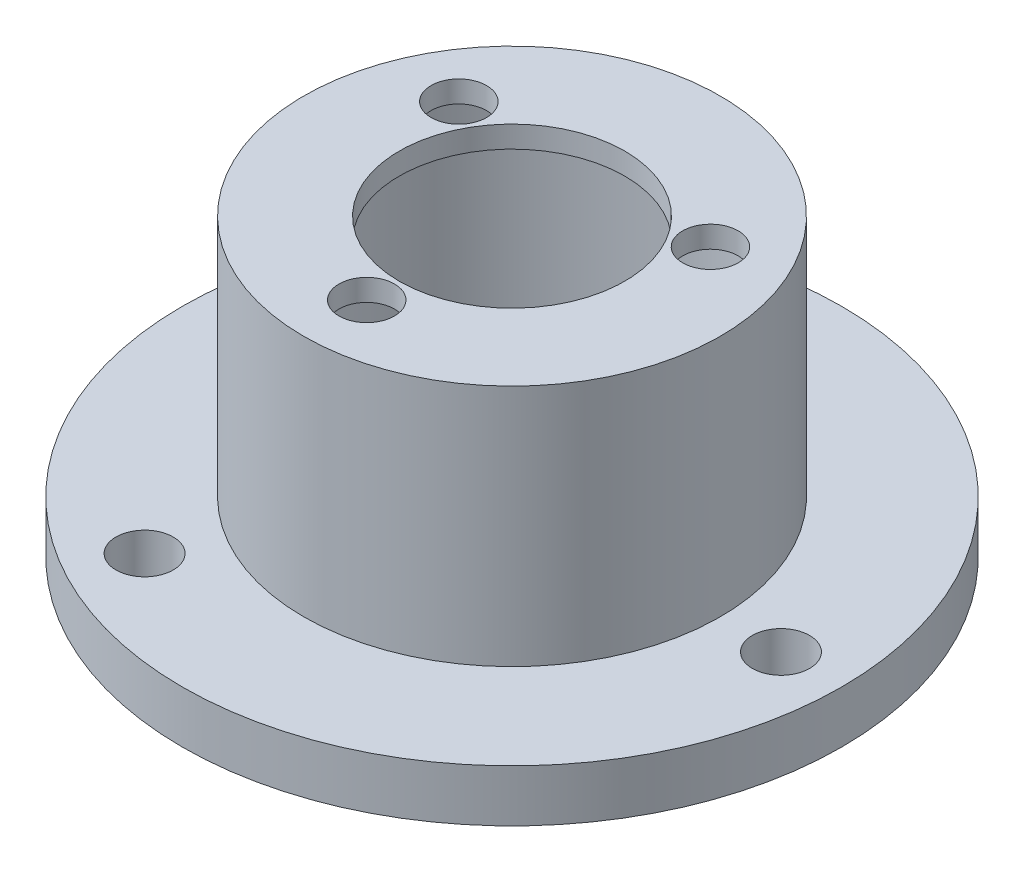
SolidWorks part; units mm, degrees
ref_plane "Front Plane" through (0, 0, 0) normal (0, 0, 1) x (1, 0, 0)
ref_plane "Top Plane" through (0, 0, 0) normal (0, 1, 0) x (1, 0, 0)
ref_plane "Right Plane" through (0, 0, 0) normal (1, 0, 0) x (0, 0, -1)
sketch "Sketch1" plane through (0, 0, 0) normal (0, 1, 0) x (1, 0, 0)
  circle A0 centre (0, 0) radius 11
  circle A1 centre (0, 0) radius 19
  dimension "D1" = 22
  dimension "D2" = 8
extrude "Boss-Extrude1" add sketch "Sketch1" along normal blind 3
sketch "Sketch2" plane through (0, 3, 0) normal (0, 1, 0) x (1, 0, 0)
  circle A0 centre (0, 0) radius 12
  circle A1 centre (0, 0) radius 11
  circle A2 centre (0, 0) radius 11 construction
  dimension "D1" = 1
extrude "Boss-Extrude2" add sketch "Sketch2" along normal blind 14
sketch "Sketch3" plane through (0, 17, 0) normal (0, 1, 0) x (1, 0, 0)
  circle A0 centre (0, 0) radius 12
  circle A1 centre (0, 0) radius 6.5
  circle A2 centre (0, 0) radius 12 construction
  dimension "D1" = 13
extrude "Boss-Extrude3" add sketch "Sketch3" against normal blind 1.25
sketch "Sketch6" plane through (0, 17, 0) normal (0, 1, 0) x (1, 0, 0)
  point P0 (-7.25, 4.1859)
  point P2 (7.25, 4.1859)
  point P4 (0, -8.3715)
  point P7 (0, 0)
  point P9 (0, -8.1154)
  point P10 (0, 0)
  dimension "D1" = 14.5
  dimension "D2" = 14.5
  dimension "D3" = 14.5
  dimension "D4" = 8.3715
  dimension "D5" = 8.3716
hole_wizard "M3 Clearance Hole1" positions "Sketch6" profile "Sketch7" hole size "M3" standard "ANSI Metric"
sketch "Sketch7" plane through (-7.25, 17, -4.1859) normal (1, 0, 0) x (0, 0, 1)
  line L0 (0, 0) -> (0, 8.4614)
  line L1 (0, 8.4614) -> (1.6, 7.5)
  line L2 (1.6, 7.5) -> (1.6, 0)
  line L5 (1.6, 0) -> (0, 0)
  line L10 (0, 8.4614) -> (-1.6, 7.5) construction
  line L11 (0, -6.35) -> (0, 107.95) construction
  dimension "Hole Dia." = 3.2
  dimension "Hole Depth" = 7.5
  dimension "Drill Angle" = 118
sketch "Sketch10" plane through (0, 3, 0) normal (0, 1, 0) x (1, 0, 0)
  line L0 (-7.75, 13.4234) -> (-7.75, -13.4234)
  line L1 (-7.75, -13.4234) -> (15.5, 0)
  line L2 (15.5, 0) -> (-7.75, 13.4234)
  circle A0 centre (0, 0) radius 15.5
  point P0 (-7.75, 13.4234)
  point P2 (-7.75, -13.4234)
  point P6 (15.5, 0)
  point P55 (-15.5, 0)
  point P56 (15.4862, 0.655)
  point P57 (0, 0)
  dimension "D1" = 31
hole_wizard "M4x0.7 Tapped Hole1" positions "Sketch10" profile "Sketch9" tap size "M4x0.7" standard "ANSI Metric" end condition up to next
sketch "Sketch9" plane through (-7.75, 3, -13.4234) normal (1, 0, 0) x (0, 0, 1)
  line L0 (0, 0) -> (0, 3)
  line L1 (0, 3) -> (1.65, 3)
  line L2 (1.65, 3) -> (1.65, 0)
  line L5 (1.65, 0) -> (0, 0)
  line L11 (0, -6.35) -> (0, 107.95) construction
  dimension "Thru Tap Drill Dia." = 3.3
  dimension "Thru Tap Drill Depth" = 3
cosmetic thread "Hole Thread1" parameters "D2"=4
cosmetic thread "Hole Thread2" parameters "D2"=4
cosmetic thread "Hole Thread3" parameters "D2"=4
cosmetic thread "Hole Thread8" parameters "D2"=4
cosmetic thread "Hole Thread9" parameters "D2"=4
cosmetic thread "Hole Thread10" parameters "D2"=4
